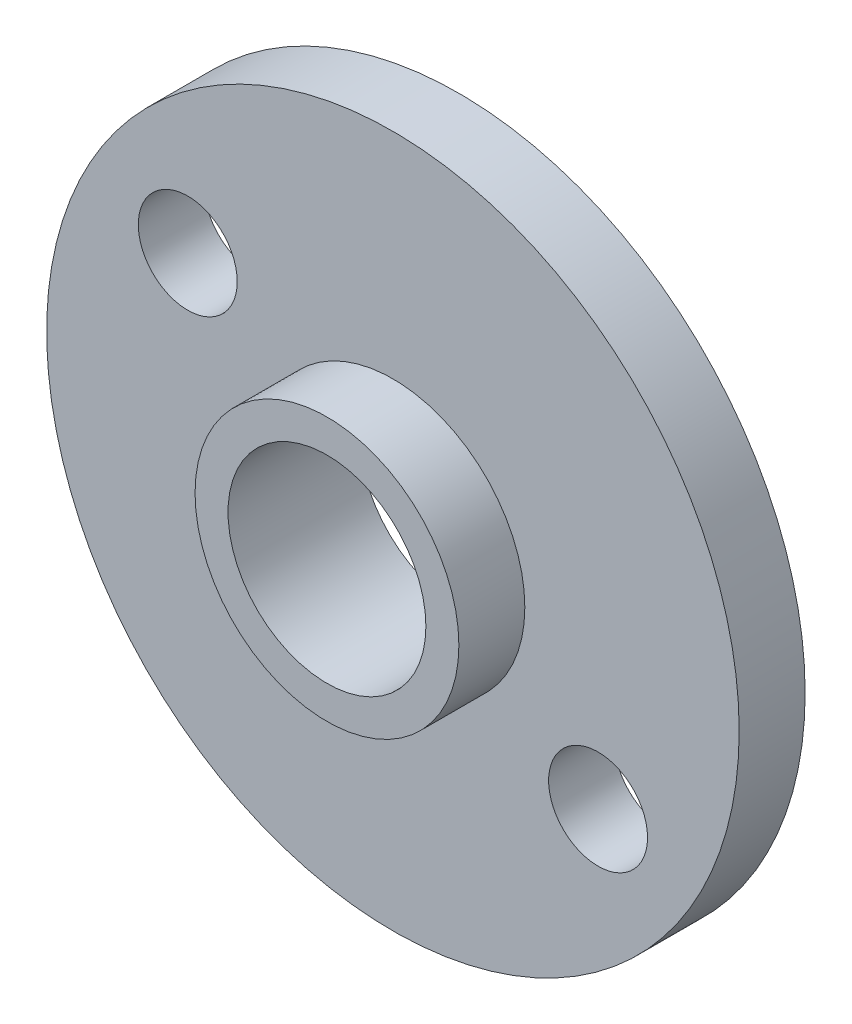
SolidWorks part; units mm, degrees
material "Resina de poliéster"
ref_plane "Alzado" through (0, 0, 0) normal (0, 0, 1) x (1, 0, 0)
ref_plane "Planta" through (0, 0, 0) normal (0, 1, 0) x (1, 0, 0)
ref_plane "Vista lateral" through (0, 0, 0) normal (1, 0, 0) x (0, 0, -1)
sketch "Model" plane through (0, 0, 0) normal (0, 0, 1) x (1, 0, 0)
  circle A136 centre (162.8, 159.5693) radius 10.5
  circle A138 centre (162.8, 159.5693) radius 3
  point P633 (152.3, 159.5693)
  point P634 (173.3, 159.5693)
  dimension "D1" = 21
extrude "Saliente-Extruir1" add sketch "Model" along normal blind 2 contours A136 A138
sketch "Croquis2" plane through (0, 0, 2) normal (0, 0, 1) x (1, 0, 0)
  circle A0 centre (156.579, 163.7584) radius 1.5 construction
  circle A1 centre (156.579, 163.7584) radius 1.5
  circle A2 centre (169.021, 155.3802) radius 1.5 construction
  circle A3 centre (169.021, 155.3802) radius 1.5
extrude "Cortar-Extruir1" cut sketch "Croquis2" against normal up to next
sketch "Croquis3" plane through (0, 0, 2) normal (0, 0, 1) x (1, 0, 0)
  circle A1 centre (162.8, 159.5693) radius 4
  circle A2 centre (162.8, 159.5693) radius 3
extrude "Saliente-Extruir2" add sketch "Croquis3" along normal blind 2
